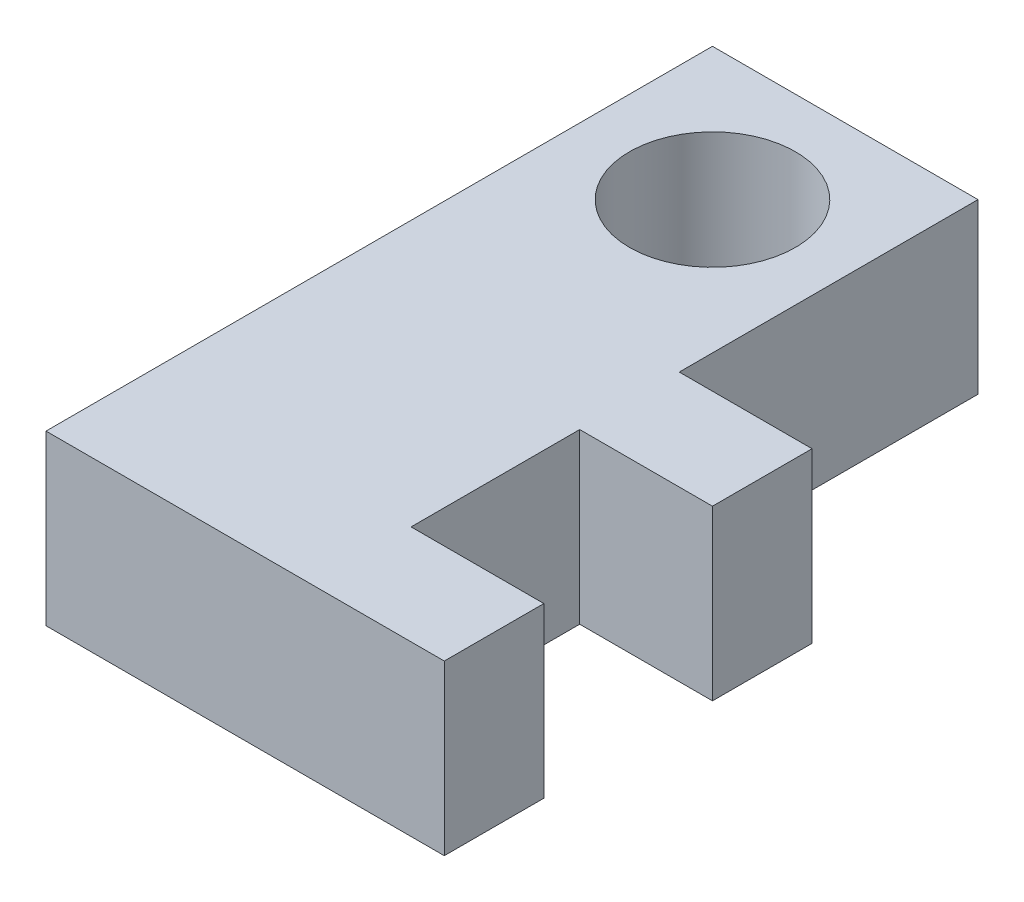
SolidWorks part; units mm, degrees
ref_plane "Front Plane" through (0, 0, 0) normal (0, 0, 1) x (1, 0, 0)
ref_plane "Top Plane" through (0, 0, 0) normal (0, 1, 0) x (1, 0, 0)
ref_plane "Right Plane" through (0, 0, 0) normal (1, 0, 0) x (0, 0, -1)
sketch "Sketch1" plane through (0, 0, 0) normal (0, 1, 0) x (1, 0, 0)
  line L1 (-4, -8) -> (4, -8)
  line L2 (-4, -8) -> (-4, 4)
  line L3 (-4, 4) -> (4, 4)
  line L4 (4, -8) -> (4, 4)
  line L5 (0, 0) -> (4, 0) construction
  line L6 (0, 0) -> (0, 4) construction
  line L7 (0, 4) -> (4, 4) construction
  line L8 (4, 0) -> (4, 4) construction
  circle A0 centre (0, 0) radius 2.5
  point P0 (0, 0)
  dimension "D2" = 5
  dimension "D1" = 8
  dimension "D3" = 12
extrude "Boss-Extrude1" add sketch "Sketch1" along normal blind 5.08
sketch "Sketch2" plane through (0, 5.08, 0) normal (0, 1, 0) x (1, 0, 0)
  line L0 (-4, -8) -> (4, -8) construction
  line L2 (-4, -13.08) -> (-4, -8)
  line L3 (-4, -8) -> (4, -8)
  line L4 (4, -13.08) -> (4, -8)
  line L5 (-4, -13.08) -> (4, -8) construction
  line L6 (-4, -8) -> (4, -13.08) construction
  line L8 (4, -8) -> (8, -8)
  line L9 (4, -8) -> (4, -5)
  line L10 (4, -5) -> (8, -5)
  line L11 (8, -8) -> (8, -5)
  line L12 (4, -13.08) -> (8, -13.08)
  line L13 (-4, -13.08) -> (-4, -16.08)
  line L14 (-4, -16.08) -> (8, -16.08)
  line L15 (8, -13.08) -> (8, -16.08)
  point P0 (0, -10.54)
  point P7 (0, 0)
  line M1 (4, -8) -> (4, 4)
  line M4 (-4, -8) -> (4, -8)
  dimension "D1" = 8
  dimension "D2" = 5.08
  dimension "D3" = 12
  dimension "D4" = 3
extrude "Boss-Extrude2" add sketch "Sketch2" against normal up to surface (5.08 mm away) contours L8 L11 L10 M1 | L15 L12 L4 L2 L13 L14 M4 up to face at (0, 0, 2)
